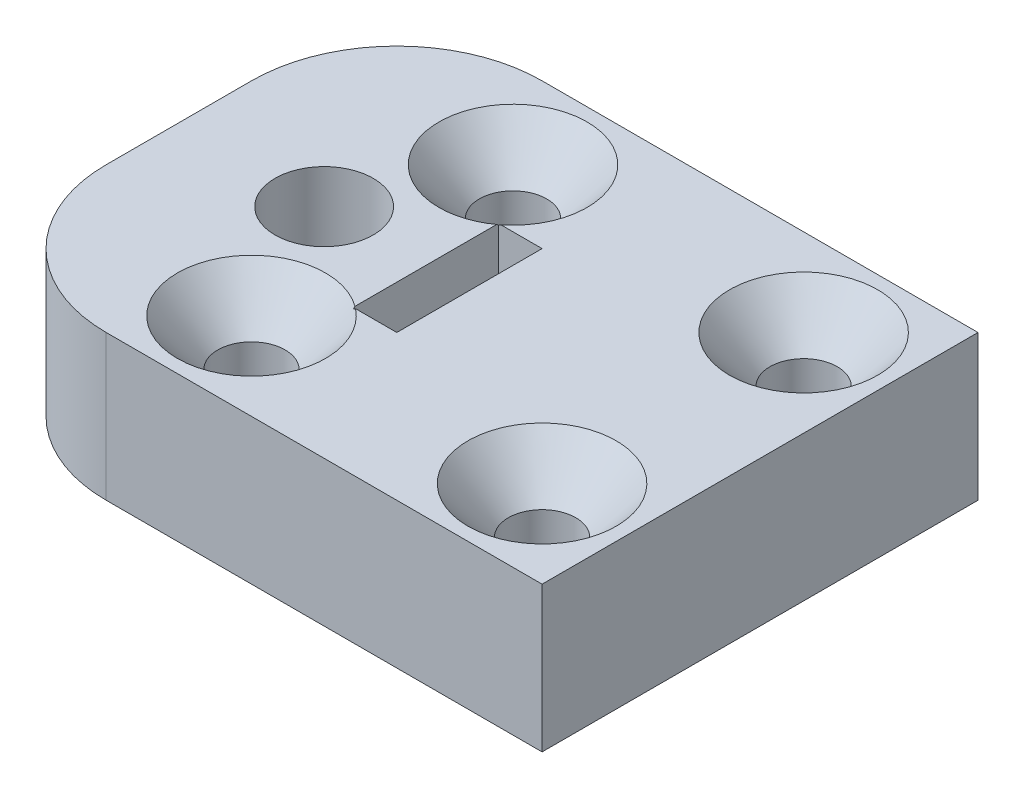
SolidWorks part; units mm, degrees
material "Acrylic (BLUE)"
ref_plane "Front Plane" through (0, 0, 0) normal (0, 0, 1) x (1, 0, 0)
ref_plane "Top Plane" through (0, 0, 0) normal (0, 1, 0) x (1, 0, 0)
ref_plane "Right Plane" through (0, 0, 0) normal (1, 0, 0) x (0, 0, -1)
sketch "Sketch1" plane through (0, 0, 0) normal (0, 1, 0) x (1, 0, 0)
  line L0 (0, 0) -> (-6.35, 0) construction
  line L1 (-6.35, 9.525) -> (19.05, 9.525)
  line L2 (-6.35, 9.525) -> (-6.35, -9.525)
  line L3 (-6.35, -9.525) -> (19.05, -9.525)
  line L4 (19.05, 9.525) -> (19.05, -9.525)
  line L5 (6.35, 3.175) -> (19.05, 3.175) construction
  line L6 (6.35, 3.175) -> (6.35, -3.175) construction
  line L7 (19.05, -3.175) -> (6.35, -3.175) construction
  line L8 (0, 0) -> (6.35, 0) construction
  line L10 (6.35, 3.175) -> (4.445, 3.175)
  line L11 (6.35, 3.175) -> (6.35, -3.175)
  line L12 (6.35, -3.175) -> (4.445, -3.175)
  line L13 (4.445, 3.175) -> (4.445, -3.175)
  circle A0 centre (0, 0) radius 2.1463
  dimension "D1" = 4.2926
  dimension "D2" = 19.05
  dimension "D3" = 6.35
  dimension "D4" = 6.35
  dimension "D5" = 25.4
  dimension "D6" = 12.7
  dimension "D7" = 1.905
extrude "Boss-Extrude1" add sketch "Sketch1" along normal blind 6.35
hole_wizard "CSK for #4 Flat Head Socket Cap Screw1" positions "Sketch4" profile "Sketch5" countersink size "#4" standard "ANSI Inch" end condition through all
sketch "Sketch4" plane through (0, 6.35, 0) normal (0, 1, 0) x (1, 0, 0)
  line L1 (2.54, 5.715) -> (15.24, 5.715)
  line L2 (2.54, 5.715) -> (2.54, -5.715)
  line L3 (2.54, -5.715) -> (15.24, -5.715)
  line L4 (15.24, 5.715) -> (15.24, -5.715)
  line L5 (0, 0) -> (2.54, 0) construction
  line L7 (-6.35, 9.525) -> (-6.35, -9.525) construction
  point P0 (2.54, 5.715)
  point P1 (15.24, -5.715)
  point P122 (2.54, -5.715)
  point P123 (15.24, 5.715)
  dimension "D1" = 8.89
  dimension "D2" = 12.7
  dimension "D3" = 11.43
sketch "Sketch5" plane through (2.54, 6.35, -5.715) normal (1, 0, 0) x (0, 0, 1)
  line L0 (0, 0) -> (0, 6.35)
  line L1 (0, 6.35) -> (1.4732, 6.35)
  line L2 (1.4732, 6.35) -> (1.4732, 2.0307)
  line L3 (1.4732, 2.0307) -> (3.2385, 0)
  line L5 (3.2385, 0) -> (0, 0)
  line L6 (-1.4732, 2.0307) -> (-3.2385, 0) construction
  line L11 (0, -6.35) -> (0, 107.95) construction
  dimension "Thru Hole Dia." = 2.9464
  dimension "Thru Hole Depth" = 6.35
  dimension "Near C'Sink Dia." = 6.477
  dimension "Near C'Sink Angle" = 82
fillet "Fillet1" radius 6.35 2 edges at (-6.35, 3.175, -9.525) (-6.35, 3.175, 9.525)
